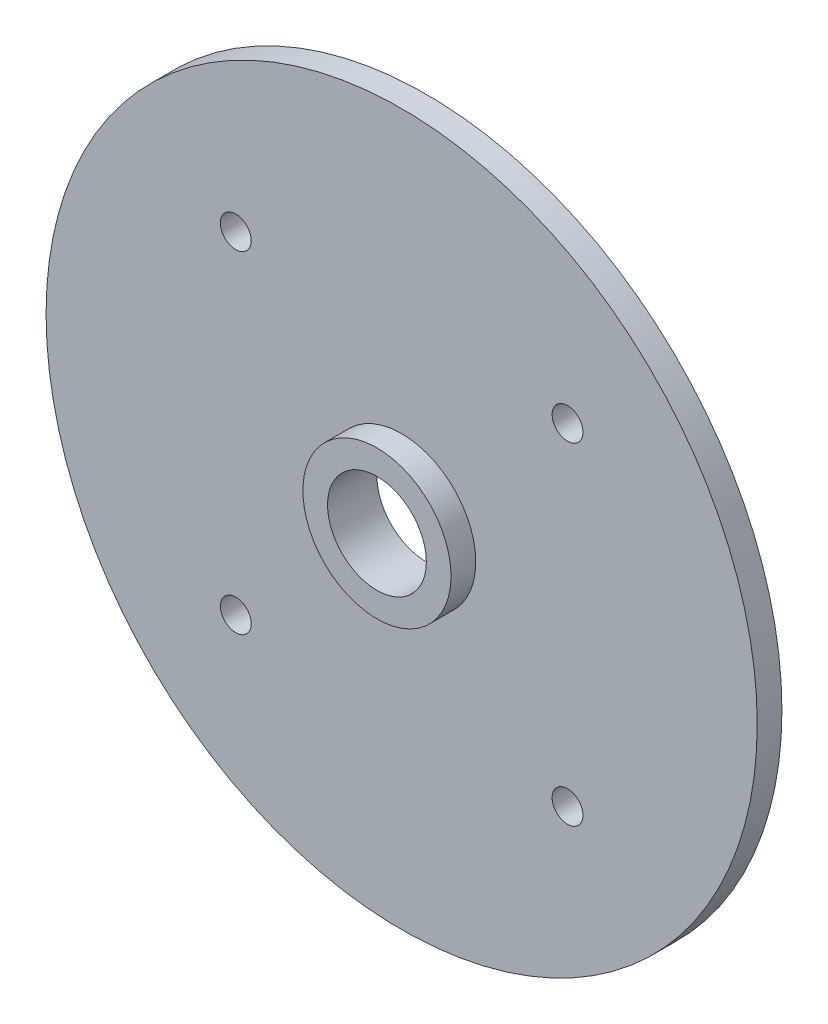
SolidWorks part; units mm, degrees
ref_plane "Front Plane" through (0, 0, 0) normal (0, 0, 1) x (1, 0, 0)
ref_plane "Top Plane" through (0, 0, 0) normal (0, 1, 0) x (1, 0, 0)
ref_plane "Right Plane" through (0, 0, 0) normal (1, 0, 0) x (0, 0, -1)
sketch "Sketch1" plane through (0, 0, 0) normal (0, 0, 1) x (1, 0, 0)
  circle A0 centre (0, -108.5) radius 6 construction
  circle A1 centre (0, -108.5) radius 6
extrude "Boss-Extrude1" add sketch "Sketch1" against normal up to vertex (2 mm away)
sketch "Sketch2" plane through (0, 0, -2) normal (0, 0, -1) x (-1, 0, 0)
  circle A0 centre (0, -108.5) radius 28.8 construction
  circle A1 centre (0, -108.5) radius 28.8
extrude "Boss-Extrude2" add sketch "Sketch2" along normal up to vertex (2 mm away)
sketch "Sketch3" plane through (0, 0, 0) normal (0, 0, 1) x (1, 0, 0)
  circle A0 centre (0, -108.5) radius 4 construction
  circle A1 centre (0, -108.5) radius 4
extrude "Cut-Extrude1" cut sketch "Sketch3" against normal through all
hole_wizard "M3x0.5 Tapped Hole1" positions "Sketch4" profile "Sketch5" tap size "M3x0.5" standard "ANSI Metric" end condition through all
sketch "Sketch4" plane through (0, 0, -2) normal (0, 0, 1) x (1, 0, 0)
  point P0 (-13.435, -95.065)
  point P3 (13.435, -95.065)
  point P6 (13.435, -121.935)
  point P9 (-13.435, -121.935)
sketch "Sketch5" plane through (-13.435, -95.065, -2) normal (1, 0, 0) x (0, -1, 0)
  line L0 (0, 0) -> (0, 2)
  line L1 (0, 2) -> (1.25, 2)
  line L2 (1.25, 2) -> (1.25, 0)
  line L5 (1.25, 0) -> (0, 0)
  line L11 (0, -6.35) -> (0, 107.95) construction
  dimension "Thru Tap Drill Dia." = 2.5
  dimension "Thru Tap Drill Depth" = 2
cosmetic thread "Hole Thread1" parameters "D2"=3
cosmetic thread "Hole Thread2" parameters "D2"=3
cosmetic thread "Hole Thread3" parameters "D2"=3
cosmetic thread "Hole Thread4" parameters "D2"=3
